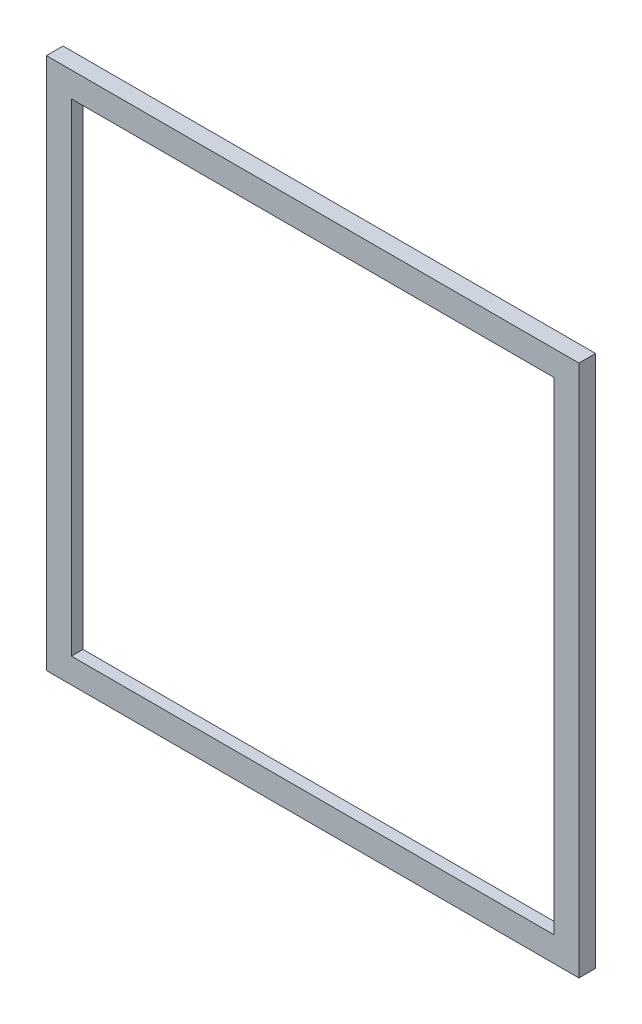
SolidWorks part; units mm, degrees
ref_plane "Alzado" through (0, 0, 0) normal (0, 0, 1) x (1, 0, 0)
ref_plane "Planta" through (0, 0, 0) normal (0, 1, 0) x (1, 0, 0)
ref_plane "Vista lateral" through (0, 0, 0) normal (1, 0, 0) x (0, 0, -1)
sketch "Croquis1" plane through (0, 0, 0) normal (0, 0, 1) x (1, 0, 0)
  line L1 (0, 0) -> (300, 0) construction
  line L2 (0, 0) -> (0, 300) construction
  line L3 (0, 300) -> (300, 300) construction
  line L4 (300, 0) -> (300, 300) construction
  line L5 (295, 5) -> (295, 295)
  line L7 (5, 5) -> (5, 295)
  line L8 (-10, 310) -> (310, 310)
  line L9 (310, -10) -> (310, 310)
  line L10 (-10, -10) -> (310, -10)
  line L11 (-10, -10) -> (-10, 310)
  line L12 (5, 295) -> (295, 295)
  line L13 (295, 5) -> (5, 5)
  line L20 (5, 295) -> (295, 295) construction
  line L23 (5, 5) -> (295, 5) construction
  dimension "D1" = 300
  dimension "D2" = 300
  dimension "D3" = 5
  dimension "D4" = 10
extrude "Saliente-Extruir1" add sketch "Croquis1" along normal blind 10
sketch "Croquis2" plane through (0, 0, 0) normal (0, 0, -1) x (-1, 0, 0)
  line L1 (0, 0) -> (-300, 0)
  line L2 (0, 0) -> (0, 300)
  line L3 (0, 300) -> (-300, 300)
  line L4 (-300, 0) -> (-300, 300)
  dimension "D1" = 300
  dimension "D2" = 300
extrude "Cortar-Extruir1" cut sketch "Croquis2" against normal blind 3
